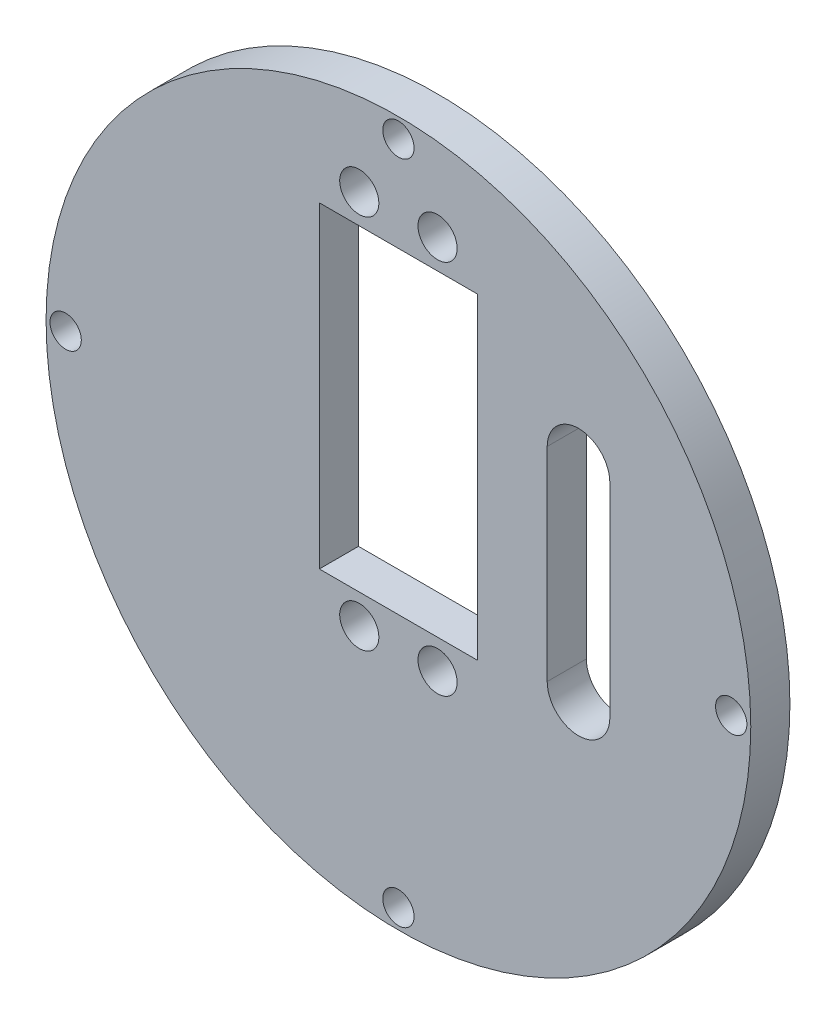
SolidWorks part; units mm, degrees
ref_plane "Front Plane" through (0, 0, 0) normal (0, 0, 1) x (1, 0, 0)
ref_plane "Top Plane" through (0, 0, 0) normal (0, 1, 0) x (1, 0, 0)
ref_plane "Right Plane" through (0, 0, 0) normal (1, 0, 0) x (0, 0, -1)
sketch "Sketch1" plane through (0, 0, 0) normal (0, 0, 1) x (1, 0, 0)
  line L0 (0, 61.1562) -> (0, -62.0155) construction
  line L1 (-10.1, 30.4) -> (10.1, 30.4)
  line L2 (-10.1, 30.4) -> (-10.1, -10.1)
  line L3 (-10.1, -10.1) -> (10.1, -10.1)
  line L4 (10.1, 30.4) -> (10.1, -10.1)
  line L5 (-10.1, 30.4) -> (10.1, -10.1) construction
  line L6 (-10.1, -10.1) -> (10.1, 30.4) construction
  line L7 (-62.9195, 0) -> (73.7046, 0) construction
  circle A0 centre (0, 0) radius 45
  circle A1 centre (0, 0) radius 1.25 construction
  circle A2 centre (-5, 34.15) radius 2.5
  circle A3 centre (5, 34.15) radius 2.5
  circle A4 centre (5, -13.85) radius 2.5
  circle A5 centre (-5, -13.85) radius 2.5
  circle A6 centre (42.5, 0) radius 2
  circle A7 centre (0, -42.5) radius 2
  circle A8 centre (-42.5, 0) radius 2
  circle A9 centre (0, 42.5) radius 2
  circle A10 centre (0, 0) radius 42.5 construction
  point P2 (0, 10.15)
  point P11 (5, -92.894)
  point P12 (5, 90.4881)
  point P13 (-96.2355, -5)
  point P14 (94.097, -5)
  point P15 (-5, -92.894)
  point P16 (-5, 90.4881)
  point P17 (-96.2355, 5)
  point P18 (94.097, 5)
  point P35 (0, 0)
  dimension "D1" = 90
  dimension "D6" = 5
  dimension "D10" = 2
  dimension "D5" = 2.5
  dimension "D14" = 4
  dimension "D13" = 85
  dimension "D2" = 20.2
  dimension "D3" = 40.5
  dimension "D7" = 3.75
  dimension "D11" = 48
  dimension "D12" = 10
  dimension "D15" = 4
  dimension "D4" = 10.1
  dimension "D8" = 5
  dimension "D9" = 2
extrude "Boss-Extrude1" add sketch "Sketch1" along normal blind 5 contours A0 A9 A8 A7 A6 A5 A4 A3 A2 L1 L4 L3 L2
sketch "Sketch2" plane through (0, 0, 5) normal (0, 0, 1) x (1, 0, 0)
  line L0 (23, 18) -> (23, -8) construction
  line L1 (27, 18) -> (27, -8)
  line L2 (19, 18) -> (19, -8)
  arc A0 (27, 18) -> (19, 18) centre (23, 18) ccw
  arc A1 (19, -8) -> (27, -8) centre (23, -8) ccw
  circle A2 centre (0, 42.5) radius 2 construction
  point P2 (23, 5)
  dimension "D1" = 4
  dimension "D4" = 18
  dimension "D2" = 23
  dimension "D3" = 5
extrude "Cut-Extrude1" cut sketch "Sketch2" against normal blind 10
